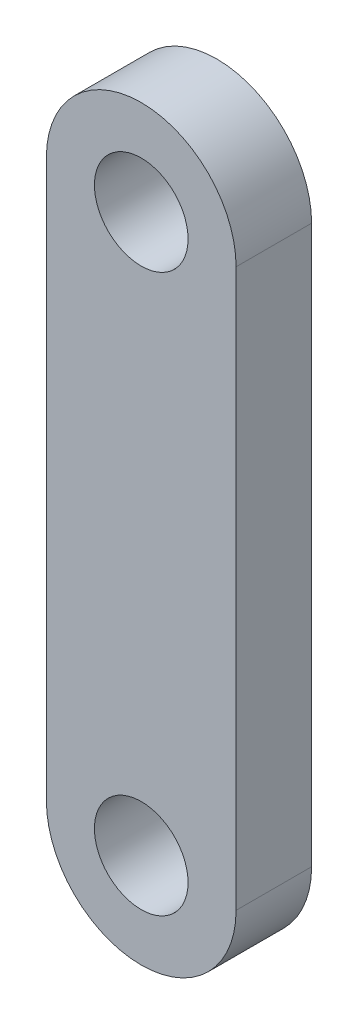
SolidWorks part; units mm, degrees
ref_plane "Front Plane" through (0, 0, 0) normal (0, 0, 1) x (1, 0, 0)
ref_plane "Top Plane" through (0, 0, 0) normal (0, 1, 0) x (1, 0, 0)
ref_plane "Right Plane" through (0, 0, 0) normal (1, 0, 0) x (0, 0, -1)
sketch "Sketch1" plane through (0, 0, 0) normal (0, 0, 1) x (1, 0, 0)
  line L0 (0, 33.503) -> (0, -13.36) construction
  line L1 (7.9756, 33.503) -> (7.9756, -13.36)
  line L2 (-7.9756, 33.503) -> (-7.9756, -13.36)
  arc A0 (7.9756, 33.503) -> (-7.9756, 33.503) centre (0, 33.503) ccw
  arc A1 (-7.9756, -13.36) -> (7.9756, -13.36) centre (0, -13.36) ccw
  circle A2 centre (0, 33.503) radius 3.937
  circle A3 centre (0, -13.36) radius 3.937
  point P3 (0, 10.0715)
  dimension "D1" = 7.874
  dimension "D2" = 7.874
  dimension "D3" = 46.863
  dimension "D4" = 15.9512
extrude "Boss-Extrude1" add sketch "Sketch1" along normal blind 6.35
